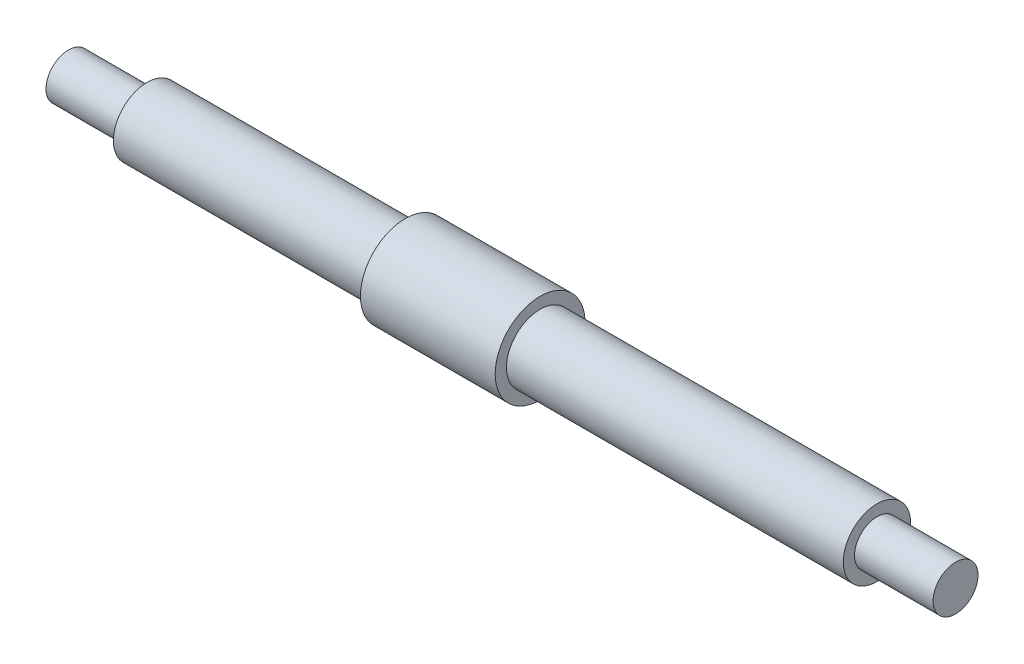
SolidWorks part; units mm, degrees
ref_plane "Plan de face" through (0, 0, 0) normal (0, 0, 1) x (1, 0, 0)
ref_plane "Plan de dessus" through (0, 0, 0) normal (0, 1, 0) x (1, 0, 0)
ref_plane "Plan de droite" through (0, 0, 0) normal (1, 0, 0) x (0, 0, -1)
sketch "Esquisse1" plane through (0, 0, 0) normal (0, 0, 1) x (1, 0, 0)
  line L0 (42, 3) -> (72, 3)
  line L1 (0, 0) -> (79, 0)
  line L2 (0, 0) -> (0, 2)
  line L3 (7, 3) -> (30, 3)
  line L4 (79, 0) -> (79, 2)
  line L6 (30, 3) -> (30, 4)
  line L7 (30, 4) -> (42, 4)
  line L8 (42, 3) -> (42, 4)
  line L11 (7, 3) -> (7, 2)
  line L12 (7, 2) -> (0, 2)
  line L14 (79, 2) -> (72, 2)
  line L17 (72, 2) -> (72, 3)
  dimension "D1" = 3
  dimension "D2" = 37
  dimension "D4" = 4
  dimension "D5" = 12
  dimension "D6" = 2
  dimension "D7" = 7
  dimension "D8" = 7
revolve "Révolution1" add sketch "Esquisse1" angle 360 about L1
